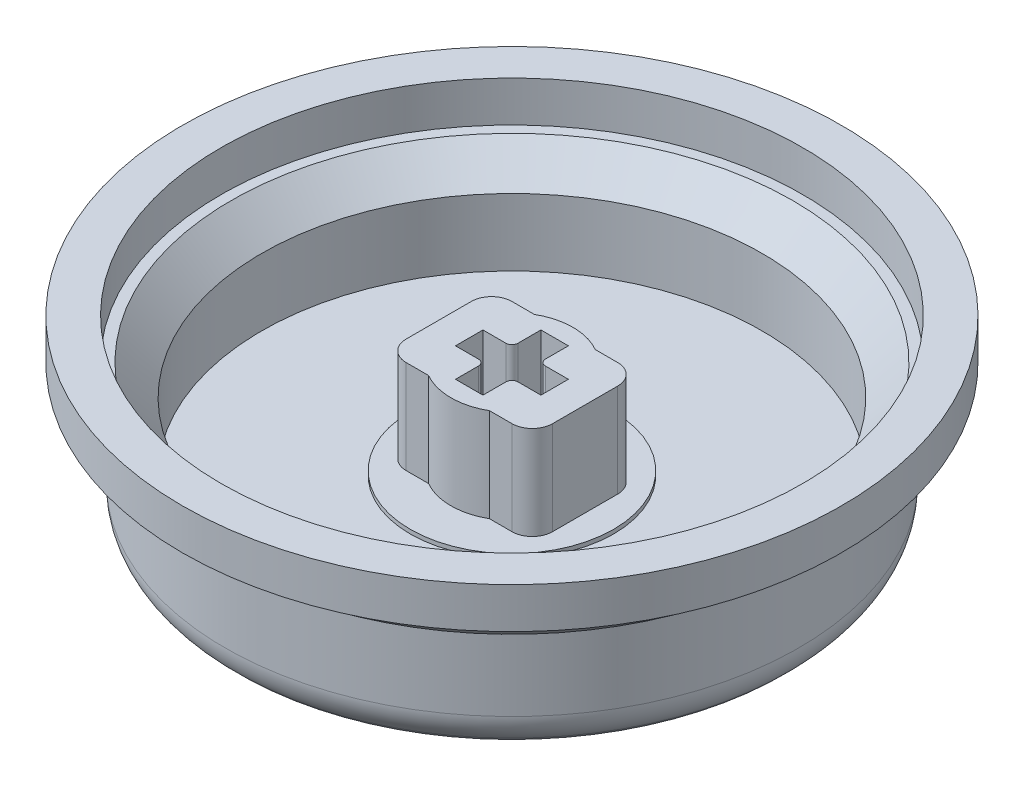
SolidWorks part; units mm, degrees
ref_plane "Front Plane" through (0, 0, 0) normal (0, 0, 1) x (1, 0, 0)
ref_plane "Top Plane" through (0, 0, 0) normal (0, 1, 0) x (1, 0, 0)
ref_plane "Right Plane" through (0, 0, 0) normal (1, 0, 0) x (0, 0, -1)
sketch "Sketch1" plane through (0, 0, 0) normal (0, 1, 0) x (1, 0, 0)
  circle A0 centre (0, 0) radius 14.1
  dimension "D1" = 28.2
extrude "button top" add sketch "Sketch1" along normal blind 1.8
sketch "Sketch2" plane through (0, 1.8, 0) normal (0, 1, 0) x (1, 0, 0)
  circle A3 centre (0, 0) radius 14.1
  circle A4 centre (0, 0) radius 14.1 construction
  circle A5 centre (0, 0) radius 12.3
  dimension "D1" = 1.8
extrude "button walls" add sketch "Sketch2" along normal blind 4.8
sketch "Sketch5" plane through (0, 1.8, 0) normal (0, 1, 0) x (1, 0, 0)
  circle A0 centre (0, 0) radius 5
  dimension "D1" = 10
extrude "offset" add sketch "Sketch5" along normal blind 0.2
sketch "Sketch3" plane through (0, 1.8, 0) normal (0, 1, 0) x (1, 0, 0)
  line L0 (0, -2.1) -> (0, 2.1) construction
  line L1 (-2.1, 0) -> (2.1, 0) construction
  line L2 (-0.675, 0.975) -> (-0.675, 2.1)
  line L3 (-0.675, -2.1) -> (0.675, -2.1)
  line L4 (-0.675, -2.1) -> (-0.675, -0.975)
  line L5 (-0.675, 2.1) -> (0.675, 2.1)
  line L6 (0.675, -2.1) -> (0.675, -0.975)
  line L7 (-0.675, -2.1) -> (0.675, 2.1) construction
  line L8 (-0.675, 2.1) -> (0.675, -2.1) construction
  line L9 (-2.1, -0.675) -> (-0.975, -0.675)
  line L10 (-2.1, -0.675) -> (-2.1, 0.675)
  line L11 (-2.1, 0.675) -> (-0.975, 0.675)
  line L12 (2.1, -0.675) -> (2.1, 0.675)
  line L13 (-2.1, -0.675) -> (2.1, 0.675) construction
  line L14 (-2.1, 0.675) -> (2.1, -0.675) construction
  line L15 (0.975, 0.675) -> (2.1, 0.675)
  line L16 (0.675, 0.975) -> (0.675, 2.1)
  line L17 (0.975, -0.675) -> (2.1, -0.675)
  line L19 (-3.6, -2.6) -> (3.6, -2.6)
  line L20 (-3.6, -2.6) -> (-3.6, 2.6)
  line L21 (-3.6, 2.6) -> (3.6, 2.6)
  line L22 (3.6, -2.6) -> (3.6, 2.6)
  line L23 (-3.6, -2.6) -> (3.6, 2.6) construction
  line L24 (-3.6, 2.6) -> (3.6, -2.6) construction
  arc A1 (-0.675, -0.975) -> (-0.975, -0.675) centre (-0.975, -0.975) ccw
  arc A2 (0.675, -0.975) -> (0.975, -0.675) centre (0.975, -0.975) cw
  arc A3 (0.975, 0.675) -> (0.675, 0.975) centre (0.975, 0.975) cw
  arc A4 (-0.675, 0.975) -> (-0.975, 0.675) centre (-0.975, 0.975) cw
  circle A5 centre (0, 0) radius 3
  point P0 (0, 0)
  point P6 (0, 0)
  point P9 (0, 0)
  point P22 (2.1, 0)
  point P24 (0, 2.1)
  point P29 (0.675, -0.675)
  point P32 (0.675, 0.675)
  dimension "D1" = 7.2
  dimension "D4" = 0.3
  dimension "D6" = 6
  dimension "D2" = 4.2
  dimension "D3" = 1.35
  dimension "D5" = 5.2
extrude "stem housing" add sketch "Sketch3" along normal blind 4.6 from surface at 0.2 contours A5 L21 L20 L19 | L19 A5 L21 A4 L2 L5 L16 A3 L15 L12 L17 A2 L6 L3 L4 A1 L9 L10 L11 | A5 L19 L22 L21 | L21 A5 | L19 A5 starting at face at (0, 2, 5)
sketch "Sketch4" plane through (0, 1.8, 0) normal (0, 1, 0) x (1, 0, 0)
  line L0 (0, 3.3382) -> (0, 12.3) construction
  line L1 (-0.8, 3.3382) -> (-0.8, 12.3)
  line L2 (0.8, 3.3382) -> (0.8, 12.3)
  line L3 (2.8909, 1.6691) -> (10.6521, 6.15) construction
  line L4 (2.4909, 2.3619) -> (10.2521, 6.8428)
  line L5 (3.2909, 0.9763) -> (11.0521, 5.4572)
  line L6 (2.8909, -1.6691) -> (10.6521, -6.15) construction
  line L7 (3.2909, -0.9763) -> (11.0521, -5.4572)
  line L8 (2.4909, -2.3619) -> (10.2521, -6.8428)
  line L9 (0, -3.3382) -> (0, -12.3) construction
  line L10 (0.8, -3.3382) -> (0.8, -12.3)
  line L11 (-0.8, -3.3382) -> (-0.8, -12.3)
  line L12 (-2.8909, -1.6691) -> (-10.6521, -6.15) construction
  line L13 (-2.4909, -2.3619) -> (-10.2521, -6.8428)
  line L14 (-3.2909, -0.9763) -> (-11.0521, -5.4572)
  line L15 (-2.8909, 1.6691) -> (-10.6521, 6.15) construction
  line L16 (-3.2909, 0.9763) -> (-11.0521, 5.4572)
  line L17 (-2.4909, 2.3619) -> (-10.2521, 6.8428)
  circle A2 centre (0, 0) radius 12.3 construction
  arc A3 (-0.8, 3.3382) -> (0.8, 3.3382) centre (0, 3.3382) ccw
  arc A4 (0.8, 12.3) -> (-0.8, 12.3) centre (0, 12.3) ccw
  arc A5 (2.4909, 2.3619) -> (3.2909, 0.9763) centre (2.8909, 1.6691) ccw
  arc A6 (11.0521, 5.4572) -> (10.2521, 6.8428) centre (10.6521, 6.15) ccw
  arc A7 (3.2909, -0.9763) -> (2.4909, -2.3619) centre (2.8909, -1.6691) ccw
  arc A8 (10.2521, -6.8428) -> (11.0521, -5.4572) centre (10.6521, -6.15) ccw
  arc A9 (0.8, -3.3382) -> (-0.8, -3.3382) centre (0, -3.3382) ccw
  arc A10 (-0.8, -12.3) -> (0.8, -12.3) centre (0, -12.3) ccw
  arc A11 (-2.4909, -2.3619) -> (-3.2909, -0.9763) centre (-2.8909, -1.6691) ccw
  arc A12 (-11.0521, -5.4572) -> (-10.2521, -6.8428) centre (-10.6521, -6.15) ccw
  arc A13 (-3.2909, 0.9763) -> (-2.4909, 2.3619) centre (-2.8909, 1.6691) ccw
  arc A14 (-10.2521, 6.8428) -> (-11.0521, 5.4572) centre (-10.6521, 6.15) ccw
  point P9 (0, 7.8191)
  point P18 (6.7715, 3.9095)
  point P25 (6.7715, -3.9095)
  point P32 (0, -7.8191)
  point P39 (-6.7715, -3.9095)
  point P46 (-6.7715, 3.9095)
  point P51 (0, 0)
  dimension "D1" = 1.6
  dimension "D2" = 6
extrude "spokes" [suppressed] add sketch "Sketch4" along normal up to surface (0.2 mm away)
fillet "Fillet1" [suppressed] radius 1.5
chamfer "Chamfer1" distance 1.5 angle 45 1 edges at (0, 6.6, 12.3)
fillet "Fillet2" radius 1 4 edges at (-3.6, 4.3, -2.6) (-3.6, 4.3, 2.6) (3.6, 4.3, -2.6) (3.6, 4.3, 2.6)
ref_axis "Axis1" through (0, 0, 0) along (0, 1, 0)
sketch "Sketch6" plane through (0, 0, 0) normal (0, 0, 1) x (1, 0, 0)
  line L0 (-13.3615, 0) -> (-13.5615, 0.2)
  line L1 (-14.1, 0) -> (14.1, 0) construction
  line L2 (-14.1, 6.6) -> (-14.1, 0) construction
  line L3 (-14.1, 1.5) -> (-14.1, 0)
  line L4 (-14.1, 0) -> (-13.3615, 0)
  arc A0 (-13.5615, 0.2) -> (-14.1, 1.5) centre (-12.2615, 1.5) cw
  dimension "D1" = 0.2
  dimension "D2" = 1.5
  dimension "D3" = 45
revolve "Cut-Revolve1" cut sketch "Sketch6" angle 360 about axis through (0, 0, 0) along (0, 1, 0)
sketch "Sketch7" plane through (0, 0, 0) normal (0, 0, 1) x (1, 0, 0)
  line L0 (14.1, 6.6) -> (15.7, 6.6)
  line L1 (15.7, 6.6) -> (14.1, 5)
  line L2 (14.1, 1.5) -> (14.1, 6.6) construction
  line L3 (14.1, 5) -> (14.1, 6.6)
  dimension "D1" = 45
  dimension "D2" = 1.6
revolve "Revolve1" add sketch "Sketch7" angle 360 about axis through (0, 0, 0) along (0, 1, 0)
sketch "Sketch8" plane through (0, 6.6, 0) normal (0, 1, 0) x (1, 0, 0)
  circle A0 centre (0, 0) radius 14.3
  circle A1 centre (0, 0) radius 16.2
extrude "Boss-Extrude1" add sketch "Sketch8" along normal blind 2
